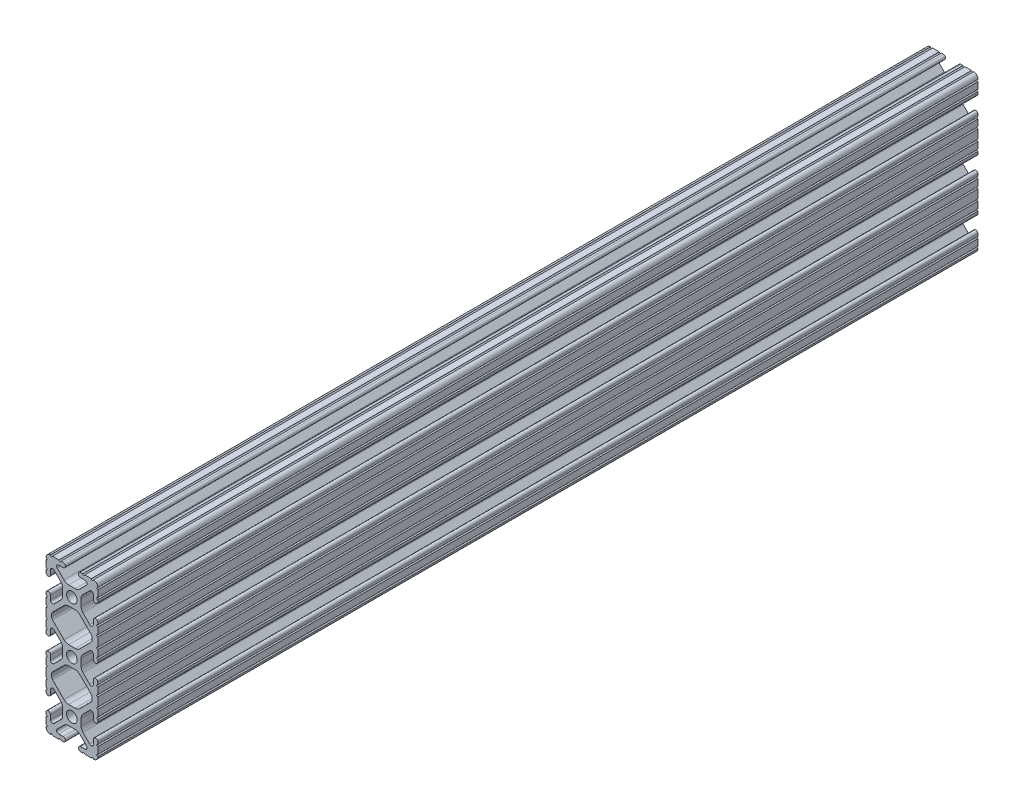
SolidWorks part; units mm, degrees
ref_plane "Front Plane" through (0, 0, 0) normal (0, 0, 1) x (1, 0, 0)
ref_plane "Top Plane" through (0, 0, 0) normal (0, 1, 0) x (1, 0, 0)
ref_plane "Right Plane" through (0, 0, 0) normal (1, 0, 0) x (0, 0, -1)
ref_plane "Plane1" through (0, 0, 431.8) normal (0, 0, 1) x (1, 0, 0)
sketch "Sketch1" plane through (0, 0, 431.8) normal (0, 0, 1) x (1, 0, 0)
  line L0 (-9.9314, 12.1463) -> (-9.9314, 13.2537)
  line L1 (-9.4702, 14.3673) -> (-3.8759, 19.9616)
  line L2 (-1.6308, 20.8915) -> (1.6308, 20.8915)
  line L3 (3.8759, 19.9616) -> (9.4702, 14.3673)
  line L4 (9.9314, 13.2537) -> (9.9314, 12.1463)
  line L5 (9.4702, 11.0327) -> (3.8759, 5.4384)
  line L6 (1.6308, 4.5085) -> (-1.6308, 4.5085)
  line L7 (-3.8759, 5.4384) -> (-9.4702, 11.0327)
  line L8 (-9.9314, -13.2537) -> (-9.9314, -12.1463)
  line L9 (-9.4702, -11.0327) -> (-3.8759, -5.4384)
  line L10 (-1.6308, -4.5085) -> (1.6308, -4.5085)
  line L11 (3.8759, -5.4384) -> (9.4702, -11.0327)
  line L12 (9.9314, -12.1463) -> (9.9314, -13.2537)
  line L13 (9.4702, -14.3673) -> (3.8759, -19.9616)
  line L14 (1.6308, -20.8915) -> (-1.6308, -20.8915)
  line L15 (-3.8759, -19.9616) -> (-9.4702, -14.3673)
  line L16 (-6.3246, 38.1) -> (-9.5504, 38.1)
  line L17 (-12.7, 34.9504) -> (-12.7, 31.7246)
  line L18 (-12.7, 30.7086) -> (-12.7, 29.7023)
  line L19 (-10.4902, 29.7023) -> (-10.4902, 31.8748)
  line L20 (-8.7558, 32.5932) -> (-5.4384, 29.2759)
  line L21 (-4.5085, 27.0308) -> (-4.5085, 23.7692)
  line L22 (-5.4384, 21.5241) -> (-8.7558, 18.2068)
  line L23 (-10.4902, 18.9252) -> (-10.4902, 21.0977)
  line L24 (-12.7, 21.0977) -> (-12.7, 20.0914)
  line L25 (-12.7, 19.0754) -> (-12.7, 15.8496)
  line L26 (-12.7, 14.8336) -> (-12.7, 10.5664)
  line L27 (-12.7, 9.5504) -> (-12.7, 6.3246)
  line L28 (-12.7, 5.3086) -> (-12.7, 4.3023)
  line L29 (-10.4902, 4.3023) -> (-10.4902, 6.4748)
  line L30 (-8.7558, 7.1932) -> (-5.4384, 3.8759)
  line L31 (-4.5085, 1.6308) -> (-4.5085, -1.6308)
  line L32 (-5.4384, -3.8759) -> (-8.7558, -7.1932)
  line L33 (-10.4902, -6.4748) -> (-10.4902, -4.3023)
  line L34 (-12.7, -4.3023) -> (-12.7, -5.3086)
  line L35 (-12.7, -6.3246) -> (-12.7, -9.5504)
  line L36 (-12.7, -10.5664) -> (-12.7, -14.8336)
  line L37 (-12.7, -15.8496) -> (-12.7, -19.0754)
  line L38 (-12.7, -20.0914) -> (-12.7, -21.0977)
  line L39 (-10.4902, -21.0977) -> (-10.4902, -18.9252)
  line L40 (-8.7558, -18.2068) -> (-5.4384, -21.5241)
  line L41 (-4.5085, -23.7692) -> (-4.5085, -27.0308)
  line L42 (-5.4384, -29.2759) -> (-8.7558, -32.5932)
  line L43 (-10.4902, -31.8748) -> (-10.4902, -29.7023)
  line L44 (-12.7, -29.7023) -> (-12.7, -30.7086)
  line L45 (-12.7, -31.7246) -> (-12.7, -34.9504)
  line L46 (-9.5504, -38.1) -> (-6.3246, -38.1)
  line L47 (-5.3086, -38.1) -> (-4.3023, -38.1)
  line L48 (-4.3023, -35.8902) -> (-6.4748, -35.8902)
  line L49 (-7.1932, -34.1558) -> (-3.8759, -30.8384)
  line L50 (-1.6308, -29.9085) -> (1.6308, -29.9085)
  line L51 (3.8759, -30.8384) -> (7.1932, -34.1558)
  line L52 (6.4748, -35.8902) -> (4.3023, -35.8902)
  line L53 (4.3023, -38.1) -> (5.3086, -38.1)
  line L54 (6.3246, -38.1) -> (9.5504, -38.1)
  line L55 (12.7, -34.9504) -> (12.7, -31.7246)
  line L56 (12.7, -30.7086) -> (12.7, -29.7023)
  line L57 (10.4902, -29.7023) -> (10.4902, -31.8748)
  line L58 (8.7558, -32.5932) -> (5.4384, -29.2759)
  line L59 (4.5085, -27.0308) -> (4.5085, -23.7692)
  line L60 (5.4384, -21.5241) -> (8.7558, -18.2068)
  line L61 (10.4902, -18.9252) -> (10.4902, -21.0977)
  line L62 (12.7, -21.0977) -> (12.7, -20.0914)
  line L63 (12.7, -19.0754) -> (12.7, -15.8496)
  line L64 (12.7, -14.8336) -> (12.7, -10.5664)
  line L65 (12.7, -9.5504) -> (12.7, -6.3246)
  line L66 (12.7, -5.3086) -> (12.7, -4.3023)
  line L67 (10.4902, -4.3023) -> (10.4902, -6.4748)
  line L68 (8.7558, -7.1932) -> (5.4384, -3.8759)
  line L69 (4.5085, -1.6308) -> (4.5085, 1.6308)
  line L70 (5.4384, 3.8759) -> (8.7558, 7.1932)
  line L71 (10.4902, 6.4748) -> (10.4902, 4.3023)
  line L72 (12.7, 4.3023) -> (12.7, 5.3086)
  line L73 (12.7, 6.3246) -> (12.7, 9.5504)
  line L74 (12.7, 10.5664) -> (12.7, 14.8336)
  line L75 (12.7, 15.8496) -> (12.7, 19.0754)
  line L76 (12.7, 20.0914) -> (12.7, 21.0977)
  line L77 (10.4902, 21.0977) -> (10.4902, 18.9252)
  line L78 (8.7558, 18.2068) -> (5.4384, 21.5241)
  line L79 (4.5085, 23.7692) -> (4.5085, 27.0308)
  line L80 (5.4384, 29.2759) -> (8.7558, 32.5932)
  line L81 (10.4902, 31.8748) -> (10.4902, 29.7023)
  line L82 (12.7, 29.7023) -> (12.7, 30.7086)
  line L83 (12.7, 31.7246) -> (12.7, 34.9504)
  line L84 (9.5504, 38.1) -> (6.3246, 38.1)
  line L85 (5.3086, 38.1) -> (4.3023, 38.1)
  line L86 (4.3023, 35.8902) -> (6.4748, 35.8902)
  line L87 (7.1932, 34.1558) -> (3.8759, 30.8384)
  line L88 (1.6308, 29.9085) -> (-1.6308, 29.9085)
  line L89 (-3.8759, 30.8384) -> (-7.1932, 34.1558)
  line L90 (-6.4748, 35.8902) -> (-4.3023, 35.8902)
  line L91 (-4.3023, 38.1) -> (-5.3086, 38.1)
  circle A0 centre (0, 25.4) radius 2.6035
  arc A1 (-9.9314, 13.2537) -> (-9.4702, 14.3673) centre (-8.3566, 13.2537) cw
  arc A2 (-3.8759, 19.9616) -> (-1.6308, 20.8915) centre (-1.6308, 17.7165) cw
  arc A3 (1.6308, 20.8915) -> (3.8759, 19.9616) centre (1.6308, 17.7165) cw
  arc A4 (9.4702, 14.3673) -> (9.9314, 13.2537) centre (8.3566, 13.2537) cw
  arc A5 (9.9314, 12.1463) -> (9.4702, 11.0327) centre (8.3566, 12.1463) cw
  arc A6 (3.8759, 5.4384) -> (1.6308, 4.5085) centre (1.6308, 7.6835) cw
  arc A7 (-1.6308, 4.5085) -> (-3.8759, 5.4384) centre (-1.6308, 7.6835) cw
  arc A8 (-9.4702, 11.0327) -> (-9.9314, 12.1463) centre (-8.3566, 12.1463) cw
  arc A9 (-9.9314, -12.1463) -> (-9.4702, -11.0327) centre (-8.3566, -12.1463) cw
  arc A10 (-3.8759, -5.4384) -> (-1.6308, -4.5085) centre (-1.6308, -7.6835) cw
  arc A11 (1.6308, -4.5085) -> (3.8759, -5.4384) centre (1.6308, -7.6835) cw
  arc A12 (9.4702, -11.0327) -> (9.9314, -12.1463) centre (8.3566, -12.1463) cw
  arc A13 (9.9314, -13.2537) -> (9.4702, -14.3673) centre (8.3566, -13.2537) cw
  arc A14 (3.8759, -19.9616) -> (1.6308, -20.8915) centre (1.6308, -17.7165) cw
  arc A15 (-1.6308, -20.8915) -> (-3.8759, -19.9616) centre (-1.6308, -17.7165) cw
  arc A16 (-9.4702, -14.3673) -> (-9.9314, -13.2537) centre (-8.3566, -13.2537) cw
  circle A17 centre (0, -25.4) radius 2.6035
  circle A18 centre (0, 0) radius 2.6035
  arc A19 (-5.3086, 38.1) -> (-6.3246, 38.1) centre (-5.8166, 38.1) cw
  arc A20 (-9.5504, 38.1) -> (-10.5664, 38.1) centre (-10.0584, 38.1) cw
  arc A21 (-10.5664, 38.1) -> (-12.7, 35.9664) centre (-10.592, 35.992) ccw
  arc A22 (-12.7, 35.9664) -> (-12.7, 34.9504) centre (-12.7, 35.4584) cw
  arc A23 (-12.7, 31.7246) -> (-12.7, 30.7086) centre (-12.7, 31.2166) cw
  arc A24 (-12.7, 29.7023) -> (-10.4902, 29.7023) centre (-11.5951, 29.7023) ccw
  arc A25 (-10.4902, 31.8748) -> (-8.7558, 32.5932) centre (-9.4742, 31.8748) cw
  arc A26 (-5.4384, 29.2759) -> (-4.5085, 27.0308) centre (-7.6835, 27.0308) cw
  arc A27 (-4.5085, 23.7692) -> (-5.4384, 21.5241) centre (-7.6835, 23.7692) cw
  arc A28 (-8.7558, 18.2068) -> (-10.4902, 18.9252) centre (-9.4742, 18.9252) cw
  arc A29 (-10.4902, 21.0977) -> (-12.7, 21.0977) centre (-11.5951, 21.0977) ccw
  arc A30 (-12.7, 20.0914) -> (-12.7, 19.0754) centre (-12.7, 19.5834) cw
  arc A31 (-12.7, 15.8496) -> (-12.7, 14.8336) centre (-12.7, 15.3416) cw
  arc A32 (-12.7, 10.5664) -> (-12.7, 9.5504) centre (-12.7, 10.0584) cw
  arc A33 (-12.7, 6.3246) -> (-12.7, 5.3086) centre (-12.7, 5.8166) cw
  arc A34 (-12.7, 4.3023) -> (-10.4902, 4.3023) centre (-11.5951, 4.3023) ccw
  arc A35 (-10.4902, 6.4748) -> (-8.7558, 7.1932) centre (-9.4742, 6.4748) cw
  arc A36 (-5.4384, 3.8759) -> (-4.5085, 1.6308) centre (-7.6835, 1.6308) cw
  arc A37 (-4.5085, -1.6308) -> (-5.4384, -3.8759) centre (-7.6835, -1.6308) cw
  arc A38 (-8.7558, -7.1932) -> (-10.4902, -6.4748) centre (-9.4742, -6.4748) cw
  arc A39 (-10.4902, -4.3023) -> (-12.7, -4.3023) centre (-11.5951, -4.3023) ccw
  arc A40 (-12.7, -5.3086) -> (-12.7, -6.3246) centre (-12.7, -5.8166) cw
  arc A41 (-12.7, -9.5504) -> (-12.7, -10.5664) centre (-12.7, -10.0584) cw
  arc A42 (-12.7, -14.8336) -> (-12.7, -15.8496) centre (-12.7, -15.3416) cw
  arc A43 (-12.7, -19.0754) -> (-12.7, -20.0914) centre (-12.7, -19.5834) cw
  arc A44 (-12.7, -21.0977) -> (-10.4902, -21.0977) centre (-11.5951, -21.0977) ccw
  arc A45 (-10.4902, -18.9252) -> (-8.7558, -18.2068) centre (-9.4742, -18.9252) cw
  arc A46 (-5.4384, -21.5241) -> (-4.5085, -23.7692) centre (-7.6835, -23.7692) cw
  arc A47 (-4.5085, -27.0308) -> (-5.4384, -29.2759) centre (-7.6835, -27.0308) cw
  arc A48 (-8.7558, -32.5932) -> (-10.4902, -31.8748) centre (-9.4742, -31.8748) cw
  arc A49 (-10.4902, -29.7023) -> (-12.7, -29.7023) centre (-11.5951, -29.7023) ccw
  arc A50 (-12.7, -30.7086) -> (-12.7, -31.7246) centre (-12.7, -31.2166) cw
  arc A51 (-12.7, -34.9504) -> (-12.7, -35.9664) centre (-12.7, -35.4584) cw
  arc A52 (-12.7, -35.9664) -> (-10.5664, -38.1) centre (-10.592, -35.992) ccw
  arc A53 (-10.5664, -38.1) -> (-9.5504, -38.1) centre (-10.0584, -38.1) cw
  arc A54 (-6.3246, -38.1) -> (-5.3086, -38.1) centre (-5.8166, -38.1) cw
  arc A55 (-4.3023, -38.1) -> (-4.3023, -35.8902) centre (-4.3023, -36.9951) ccw
  arc A56 (-6.4748, -35.8902) -> (-7.1932, -34.1558) centre (-6.4748, -34.8742) cw
  arc A57 (-3.8759, -30.8384) -> (-1.6308, -29.9085) centre (-1.6308, -33.0835) cw
  arc A58 (1.6308, -29.9085) -> (3.8759, -30.8384) centre (1.6308, -33.0835) cw
  arc A59 (7.1932, -34.1558) -> (6.4748, -35.8902) centre (6.4748, -34.8742) cw
  arc A60 (4.3023, -35.8902) -> (4.3023, -38.1) centre (4.3023, -36.9951) ccw
  arc A61 (5.3086, -38.1) -> (6.3246, -38.1) centre (5.8166, -38.1) cw
  arc A62 (9.5504, -38.1) -> (10.5664, -38.1) centre (10.0584, -38.1) cw
  arc A63 (10.5664, -38.1) -> (12.7, -35.9664) centre (10.592, -35.992) ccw
  arc A64 (12.7, -35.9664) -> (12.7, -34.9504) centre (12.7, -35.4584) cw
  arc A65 (12.7, -31.7246) -> (12.7, -30.7086) centre (12.7, -31.2166) cw
  arc A66 (12.7, -29.7023) -> (10.4902, -29.7023) centre (11.5951, -29.7023) ccw
  arc A67 (10.4902, -31.8748) -> (8.7558, -32.5932) centre (9.4742, -31.8748) cw
  arc A68 (5.4384, -29.2759) -> (4.5085, -27.0308) centre (7.6835, -27.0308) cw
  arc A69 (4.5085, -23.7692) -> (5.4384, -21.5241) centre (7.6835, -23.7692) cw
  arc A70 (8.7558, -18.2068) -> (10.4902, -18.9252) centre (9.4742, -18.9252) cw
  arc A71 (10.4902, -21.0977) -> (12.7, -21.0977) centre (11.5951, -21.0977) ccw
  arc A72 (12.7, -20.0914) -> (12.7, -19.0754) centre (12.7, -19.5834) cw
  arc A73 (12.7, -15.8496) -> (12.7, -14.8336) centre (12.7, -15.3416) cw
  arc A74 (12.7, -10.5664) -> (12.7, -9.5504) centre (12.7, -10.0584) cw
  arc A75 (12.7, -6.3246) -> (12.7, -5.3086) centre (12.7, -5.8166) cw
  arc A76 (12.7, -4.3023) -> (10.4902, -4.3023) centre (11.5951, -4.3023) ccw
  arc A77 (10.4902, -6.4748) -> (8.7558, -7.1932) centre (9.4742, -6.4748) cw
  arc A78 (5.4384, -3.8759) -> (4.5085, -1.6308) centre (7.6835, -1.6308) cw
  arc A79 (4.5085, 1.6308) -> (5.4384, 3.8759) centre (7.6835, 1.6308) cw
  arc A80 (8.7558, 7.1932) -> (10.4902, 6.4748) centre (9.4742, 6.4748) cw
  arc A81 (10.4902, 4.3023) -> (12.7, 4.3023) centre (11.5951, 4.3023) ccw
  arc A82 (12.7, 5.3086) -> (12.7, 6.3246) centre (12.7, 5.8166) cw
  arc A83 (12.7, 9.5504) -> (12.7, 10.5664) centre (12.7, 10.0584) cw
  arc A84 (12.7, 14.8336) -> (12.7, 15.8496) centre (12.7, 15.3416) cw
  arc A85 (12.7, 19.0754) -> (12.7, 20.0914) centre (12.7, 19.5834) cw
  arc A86 (12.7, 21.0977) -> (10.4902, 21.0977) centre (11.5951, 21.0977) ccw
  arc A87 (10.4902, 18.9252) -> (8.7558, 18.2068) centre (9.4742, 18.9252) cw
  arc A88 (5.4384, 21.5241) -> (4.5085, 23.7692) centre (7.6835, 23.7692) cw
  arc A89 (4.5085, 27.0308) -> (5.4384, 29.2759) centre (7.6835, 27.0308) cw
  arc A90 (8.7558, 32.5932) -> (10.4902, 31.8748) centre (9.4742, 31.8748) cw
  arc A91 (10.4902, 29.7023) -> (12.7, 29.7023) centre (11.5951, 29.7023) ccw
  arc A92 (12.7, 30.7086) -> (12.7, 31.7246) centre (12.7, 31.2166) cw
  arc A93 (12.7, 34.9504) -> (12.7, 35.9664) centre (12.7, 35.4584) cw
  arc A94 (12.7, 35.9664) -> (10.5664, 38.1) centre (10.592, 35.992) ccw
  arc A95 (10.5664, 38.1) -> (9.5504, 38.1) centre (10.0584, 38.1) cw
  arc A96 (6.3246, 38.1) -> (5.3086, 38.1) centre (5.8166, 38.1) cw
  arc A97 (4.3023, 38.1) -> (4.3023, 35.8902) centre (4.3023, 36.9951) ccw
  arc A98 (6.4748, 35.8902) -> (7.1932, 34.1558) centre (6.4748, 34.8742) cw
  arc A99 (3.8759, 30.8384) -> (1.6308, 29.9085) centre (1.6308, 33.0835) cw
  arc A100 (-1.6308, 29.9085) -> (-3.8759, 30.8384) centre (-1.6308, 33.0835) cw
  arc A101 (-7.1932, 34.1558) -> (-6.4748, 35.8902) centre (-6.4748, 34.8742) cw
  arc A102 (-4.3023, 35.8902) -> (-4.3023, 38.1) centre (-4.3023, 36.9951) ccw
extrude "Boss-Extrude1" add sketch "Sketch1" against normal blind 431.8
